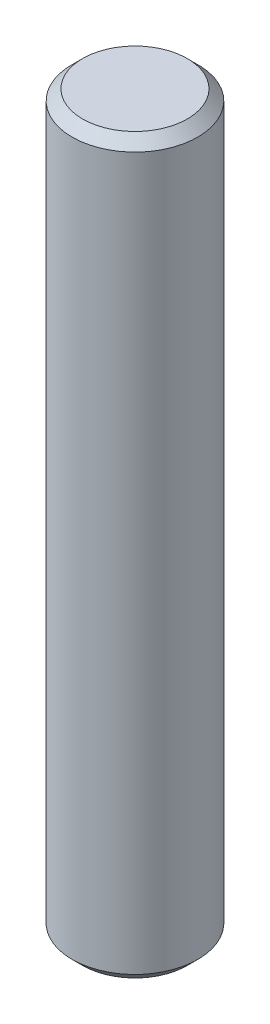
SolidWorks part; units mm, degrees
ref_plane "Front Plane" through (0, 0, 0) normal (0, 0, 1) x (1, 0, 0)
ref_plane "Top Plane" through (0, 0, 0) normal (0, 1, 0) x (1, 0, 0)
ref_plane "Right Plane" through (0, 0, 0) normal (1, 0, 0) x (0, 0, -1)
sketch "Sketch1" plane through (0, 0, 0) normal (0, 1, 0) x (1, 0, 0)
  circle A0 centre (0, 0) radius 6
  dimension "D1" = 12
extrude "Boss-Extrude1" add sketch "Sketch1" along normal mid plane 70
chamfer "Chamfer1" distance 1 angle 45 2 edges at (0, 35, 6) (0, -35, 6)
cosmetic thread "Cosmetic Thread1"
cosmetic thread "Cosmetic Thread3"
